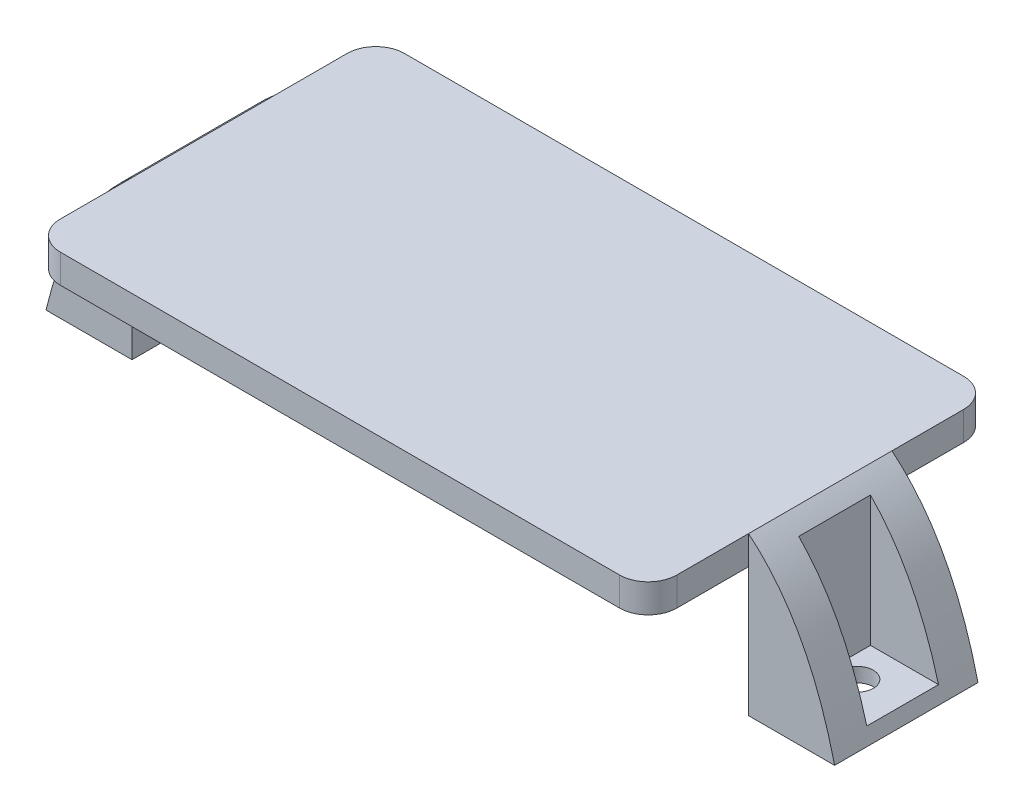
SolidWorks part; units mm, degrees
ref_plane "Front Plane" through (0, 0, 0) normal (0, 0, 1) x (1, 0, 0)
ref_plane "Top Plane" through (0, 0, 0) normal (0, 1, 0) x (1, 0, 0)
ref_plane "Right Plane" through (0, 0, 0) normal (1, 0, 0) x (0, 0, -1)
sketch "Sketch1" plane through (0, 0, 0) normal (0, 1, 0) x (1, 0, 0)
  line L1 (-27.305, -15.24) -> (27.305, -15.24)
  line L2 (-27.305, -15.24) -> (-27.305, 15.24)
  line L3 (-27.305, 15.24) -> (27.305, 15.24)
  line L4 (27.305, -15.24) -> (27.305, 15.24)
  line L5 (-27.305, -15.24) -> (27.305, 15.24) construction
  line L6 (-27.305, 15.24) -> (27.305, -15.24) construction
  point P0 (0, 0)
  dimension "D1" = 54.61
  dimension "D2" = 30.48
extrude "Boss-Extrude1" add sketch "Sketch1" against normal blind 2.54
fillet "Fillet1" radius 2.54 4 edges at (-27.305, -1.27, -15.24) (-27.305, -1.27, 15.24) (27.305, -1.27, 15.24) (27.305, -1.27, -15.24)
sketch "Sketch2" plane through (0, 0, 0) normal (0, 0, 1) x (1, 0, 0)
  line L0 (27.305, 0) -> (27.305, -13.97)
  line L1 (27.305, -13.97) -> (34.925, -13.97)
  spline S0 degree 2 poles (34.925, -13.97) (28.724, 11.9855) (0, 0) knots 0 0 0 1 1 1
  dimension "D1" = 7.62
extrude "Boss-Extrude2" add sketch "Sketch2" along normal blind 6.35 and the other way blind 6.35 contours L1 S0 L0
sketch "Sketch3" plane through (0, 0, 0) normal (0, 1, 0) x (1, 0, 0)
  line L1 (34.925, -3.175) -> (28.575, -3.175)
  line L2 (34.925, -3.175) -> (34.925, 3.175)
  line L3 (34.925, 3.175) -> (28.575, 3.175)
  line L4 (28.575, -3.175) -> (28.575, 3.175)
  dimension "D1" = 6.35
  dimension "D2" = 6.35
extrude "Cut-Extrude1" cut sketch "Sketch3" against normal blind 12.7
sketch "Sketch4" plane through (0, -13.97, 0) normal (0, -1, 0) x (-1, 0, 0)
  circle A0 centre (-30.607, 0) radius 1.397
extrude "Cut-Extrude2" cut sketch "Sketch4" against normal through all
mirror "Mirror1" about plane through (0, 0, 0) normal (1, 0, 0) of "Cut-Extrude2", "Cut-Extrude1", "Boss-Extrude2"
